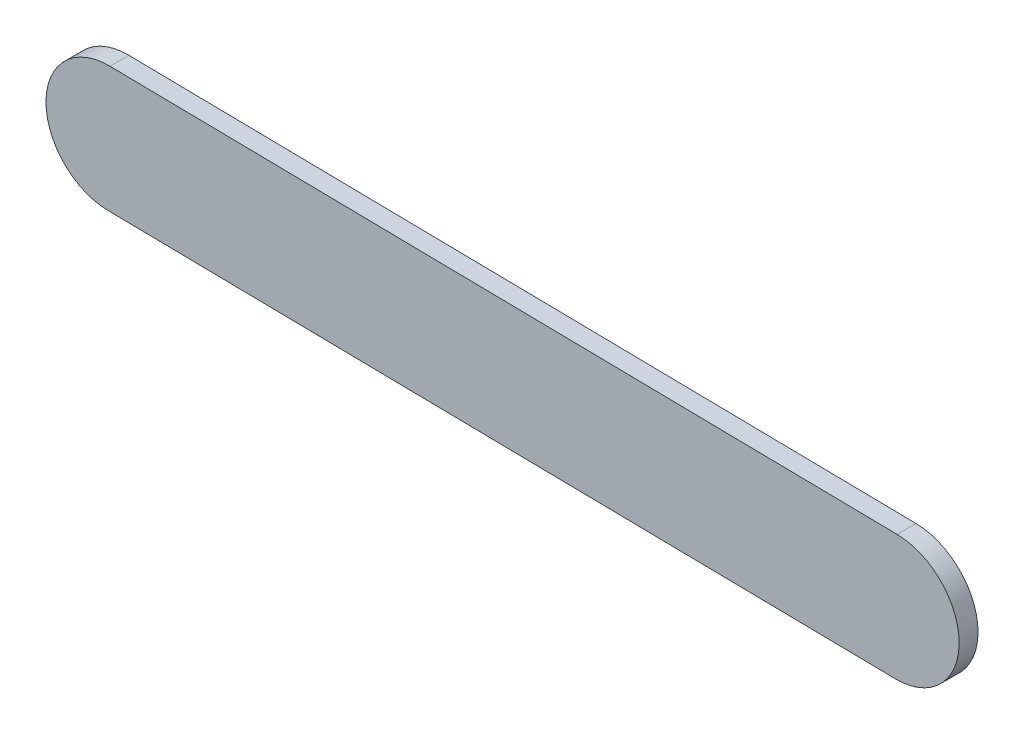
SolidWorks part; units mm, degrees
ref_plane "Front Plane" through (0, 0, 0) normal (0, 0, 1) x (1, 0, 0)
ref_plane "Top Plane" through (0, 0, 0) normal (0, 1, 0) x (1, 0, 0)
ref_plane "Right Plane" through (0, 0, 0) normal (1, 0, 0) x (0, 0, -1)
sketch "Sketch1" plane through (0, 0, 0) normal (0, 0, 1) x (1, 0, 0)
  line L0 (53.4525, 19.6302) -> (303.4239, 15.8492)
  line L1 (302.8189, -24.1462) -> (52.8475, -20.3652)
  arc A0 (303.4239, 15.8492) -> (302.8189, -24.1462) centre (303.1214, -4.1485) cw
  arc A1 (52.8475, -20.3652) -> (53.4525, 19.6302) centre (53.15, -0.3675) cw
extrude "Boss-Extrude1" add sketch "Sketch1" along normal blind 6
sketch "Sketch2" plane through (0, 0, 0) normal (0, 0, -1) x (-1, 0, 0)
  circle A0 centre (-53.15, -0.3675) radius 12.2
  dimension "D1" = 24.4
extrude "Boss-Extrude2" add sketch "Sketch2" along normal offset from surface (5.25 mm away) 0.25
